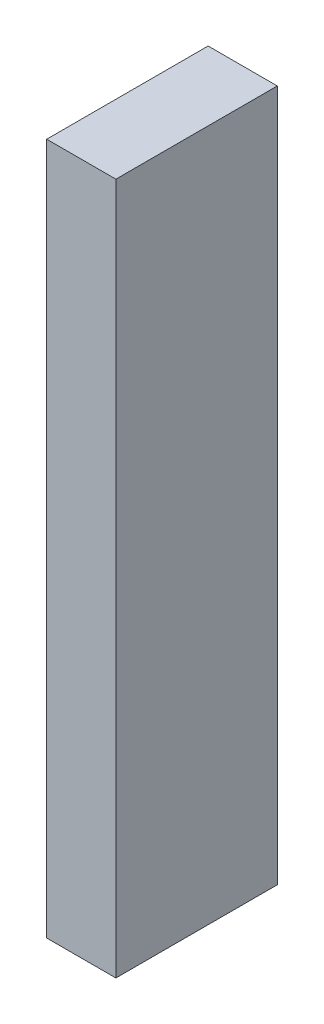
SolidWorks part; units mm, degrees
material "Balsa"
ref_plane "Front Plane" through (0, 0, 0) normal (0, 0, 1) x (1, 0, 0)
ref_plane "Top Plane" through (0, 0, 0) normal (0, 1, 0) x (1, 0, 0)
ref_plane "Right Plane" through (0, 0, 0) normal (1, 0, 0) x (0, 0, -1)
sketch "Sketch1" plane through (0, 0, 0) normal (1, 0, 0) x (0, 0, -1)
  line L1 (0, 0) -> (304.8, 0)
  line L2 (0, 0) -> (0, 304.8)
  line L3 (0, 304.8) -> (304.8, 304.8)
  line L4 (304.8, 0) -> (304.8, 304.8)
  line L5 (0, 0) -> (88.9, 0)
  line L6 (0, 0) -> (0, 304.8)
  line L7 (0, 304.8) -> (88.9, 304.8)
  line L8 (88.9, 0) -> (88.9, 304.8)
  line L9 (0, 0) -> (88.9, 0)
  line L10 (0, 0) -> (0, 381)
  line L11 (0, 381) -> (88.9, 381)
  line L12 (88.9, 0) -> (88.9, 381)
extrude "Boss-Extrude1" add sketch "Sketch1" along normal blind 38.1 contours L1 L8 L3 L2 | L3 L12 L11 L10
